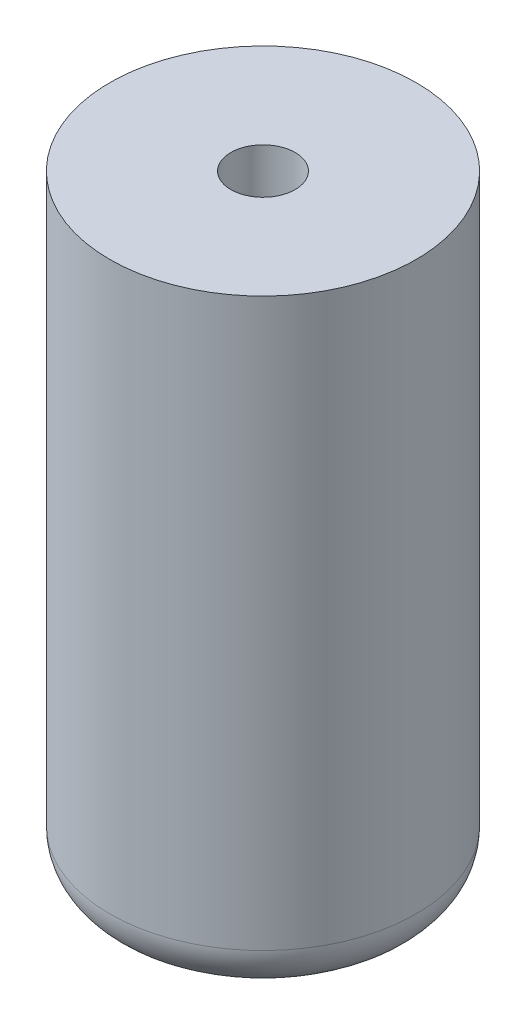
SolidWorks part; units mm, degrees
ref_plane "Front" through (0, 0, 0) normal (0, 0, 1) x (1, 0, 0)
ref_plane "Top" through (0, 0, 0) normal (0, 1, 0) x (1, 0, 0)
ref_plane "Right" through (0, 0, 0) normal (1, 0, 0) x (0, 0, -1)
sketch "Sketch1" plane through (0, 0, 0) normal (0, 1, 0) x (1, 0, 0)
  circle A0 centre (0, 0) radius 10
  dimension "D1" = 20
extrude "Boss-Extrude1" add sketch "Sketch1" along normal blind 40
fillet "Fillet1" radius 3 1 edges at (0, 0, 10)
sketch "Sketch3" plane through (0, 40, 0) normal (0, 1, 0) x (1, 0, 0)
  circle A0 centre (0, 0) radius 2.1
  dimension "D1" = 4.2
extrude "Cut-Extrude1" cut sketch "Sketch3" against normal blind 10
